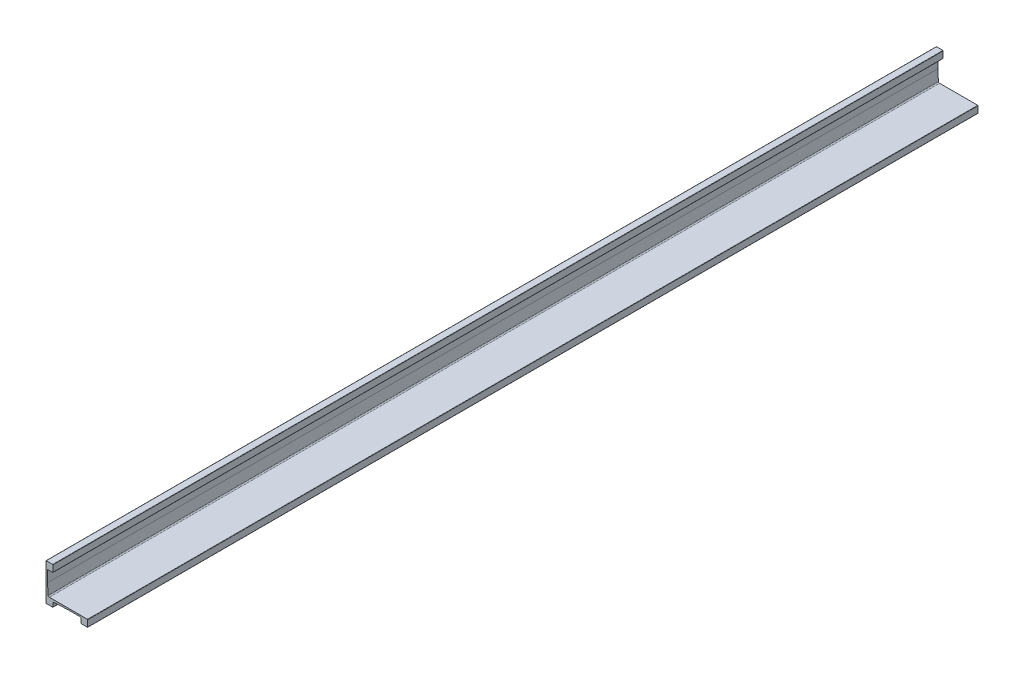
SolidWorks part; units mm, degrees
material "6061-T6 (SS)"
ref_plane "Front Plane" through (0, 0, 0) normal (0, 0, 1) x (1, 0, 0)
ref_plane "Top Plane" through (0, 0, 0) normal (0, 1, 0) x (1, 0, 0)
ref_plane "Right Plane" through (0, 0, 0) normal (1, 0, 0) x (0, 0, -1)
sketch "Sketch2" plane through (0, 0, 0) normal (0, 0, 1) x (1, 0, 0)
  line L0 (0, 0) -> (0, 50.8)
  line L1 (0, 50.8) -> (9.525, 50.8)
  line L2 (9.525, 50.8) -> (9.525, 41.275)
  line L3 (9.525, 41.275) -> (2.032, 41.275)
  line L4 (2.032, 41.275) -> (2.032, 25.4)
  line L5 (2.032, 25.4) -> (3.0734, 9.525)
  line L6 (3.0734, 9.525) -> (57.15, 9.525)
  line L7 (57.15, 9.525) -> (57.15, 0)
  line L8 (57.15, 0) -> (47.625, 0)
  line L9 (47.625, 0) -> (47.625, 7.493)
  line L10 (47.625, 7.493) -> (28.575, 7.493)
  line L12 (9.525, 6.4516) -> (9.525, 0)
  line L13 (9.525, 0) -> (0, 0)
  line L14 (28.575, 7.493) -> (9.525, 6.4516)
  dimension "D1" = 9.525
  dimension "D2" = 9.525
  dimension "D3" = 9.525
  dimension "D4" = 9.525
  dimension "D5" = 9.525
  dimension "D6" = 2.032
  dimension "D7" = 2.032
  dimension "D8" = 3.0734
  dimension "D9" = 3.0734
  dimension "D10" = 57.15
  dimension "D11" = 50.8
  dimension "D12" = 25.4
  dimension "D13" = 28.575
extrude "Boss-Extrude1" add sketch "Sketch2" along normal blind 1219.2
fillet "Fillet1" radius 0.381 10 edges at (57.15, 9.525, 609.6) (57.15, 0, 609.6) (47.625, 0, 609.6) (47.625, 7.493, 609.6) (9.525, 0, 609.6) (0, 0, 609.6) (2.032, 41.275, 609.6) (9.525, 41.275, 609.6) (9.525, 50.8, 609.6) (0, 50.8, 609.6)
fillet "Fillet2" radius 1.5875 2 edges at (9.525, 6.4516, 609.6) (3.0734, 9.525, 609.6)
